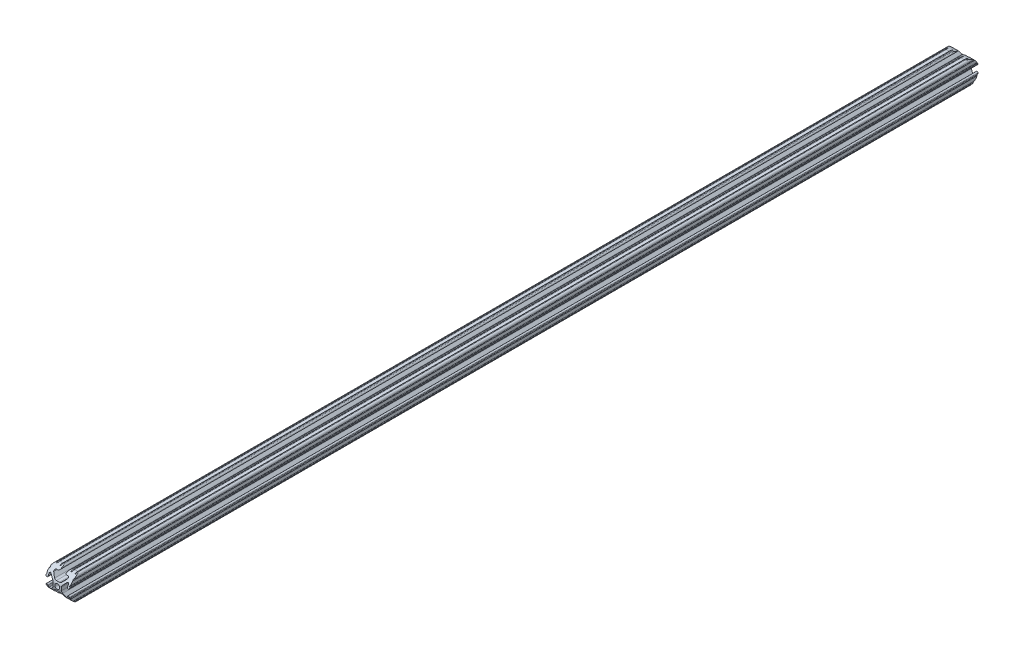
SolidWorks part; units mm, degrees
ref_plane "Front Plane" through (0, 0, 0) normal (0, 0, 1) x (1, 0, 0)
ref_plane "Top Plane" through (0, 0, 0) normal (0, 1, 0) x (1, 0, 0)
ref_plane "Right Plane" through (0, 0, 0) normal (1, 0, 0) x (0, 0, -1)
ref_plane "Plane1" through (0, 0, -450.85) normal (0, 0, -1) x (-1, 0, 0)
sketch "Sketch1" plane through (0, 0, -450.85) normal (0, 0, -1) x (-1, 0, 0)
  line L0 (12.7, -9.5504) -> (12.7, -6.3331)
  line L1 (12.7, -5.3171) -> (12.7, -4.3434)
  line L2 (10.4902, -4.3434) -> (10.4902, -6.4748)
  line L3 (8.7558, -7.1932) -> (5.4257, -3.8632)
  line L4 (4.4958, -1.6181) -> (4.4958, 1.6181)
  line L5 (5.4257, 3.8632) -> (8.7558, 7.1932)
  line L6 (10.4902, 6.4748) -> (10.4902, 4.3434)
  line L7 (12.7, 4.3434) -> (12.7, 5.3171)
  line L8 (12.7, 6.3331) -> (12.7, 9.5504)
  line L9 (9.5504, 12.7) -> (6.3331, 12.7)
  line L10 (5.3171, 12.7) -> (4.3434, 12.7)
  line L11 (4.3434, 10.4902) -> (6.4748, 10.4902)
  line L12 (7.1932, 8.7558) -> (3.8632, 5.4257)
  line L13 (1.6181, 4.4958) -> (-1.6181, 4.4958)
  line L14 (-3.8632, 5.4257) -> (-7.1932, 8.7558)
  line L15 (-6.4748, 10.4902) -> (-4.3434, 10.4902)
  line L16 (-4.3434, 12.7) -> (-5.3171, 12.7)
  line L17 (-6.3331, 12.7) -> (-9.5504, 12.7)
  line L18 (-12.7, 9.5504) -> (-12.7, 6.3331)
  line L19 (-12.7, 5.3171) -> (-12.7, 4.3434)
  line L20 (-10.4902, 4.3434) -> (-10.4902, 6.4748)
  line L21 (-8.7558, 7.1932) -> (-5.4257, 3.8632)
  line L22 (-4.4958, 1.6181) -> (-4.4958, -1.6181)
  line L23 (-5.4257, -3.8632) -> (-8.7558, -7.1932)
  line L24 (-10.4902, -6.4748) -> (-10.4902, -4.3434)
  line L25 (-12.7, -4.3434) -> (-12.7, -5.3171)
  line L26 (-12.7, -6.3331) -> (-12.7, -9.5504)
  line L27 (-9.5504, -12.7) -> (-6.3331, -12.7)
  line L28 (-5.3171, -12.7) -> (-4.3434, -12.7)
  line L29 (-4.3434, -10.4902) -> (-6.4748, -10.4902)
  line L30 (-7.1932, -8.7558) -> (-3.8632, -5.4257)
  line L31 (-1.6181, -4.4958) -> (1.6181, -4.4958)
  line L32 (3.8632, -5.4257) -> (7.1932, -8.7558)
  line L33 (6.4748, -10.4902) -> (4.3434, -10.4902)
  line L34 (4.3434, -12.7) -> (5.3171, -12.7)
  line L35 (6.3331, -12.7) -> (9.5504, -12.7)
  arc A0 (12.6998, -10.5664) -> (12.7, -9.5504) centre (12.7, -10.0584) cw
  arc A1 (12.7, -6.3331) -> (12.7, -5.3171) centre (12.7, -5.8251) cw
  arc A2 (12.7, -4.3434) -> (10.4902, -4.3434) centre (11.5951, -4.3434) ccw
  arc A3 (10.4902, -6.4748) -> (8.7558, -7.1932) centre (9.4742, -6.4748) cw
  arc A4 (5.4257, -3.8632) -> (4.4958, -1.6181) centre (7.6708, -1.6181) cw
  arc A5 (4.4958, 1.6181) -> (5.4257, 3.8632) centre (7.6708, 1.6181) cw
  arc A6 (8.7558, 7.1932) -> (10.4902, 6.4748) centre (9.4742, 6.4748) cw
  arc A7 (10.4902, 4.3434) -> (12.7, 4.3434) centre (11.5951, 4.3434) ccw
  arc A8 (12.7, 5.3171) -> (12.7, 6.3331) centre (12.7, 5.8251) cw
  arc A9 (12.7, 9.5504) -> (12.6998, 10.5664) centre (12.7, 10.0584) cw
  arc A10 (12.6998, 10.5664) -> (10.5664, 12.6998) centre (10.5918, 10.5918) ccw
  arc A11 (10.5664, 12.6998) -> (9.5504, 12.7) centre (10.0584, 12.7) cw
  arc A12 (6.3331, 12.7) -> (5.3171, 12.7) centre (5.8251, 12.7) cw
  arc A13 (4.3434, 12.7) -> (4.3434, 10.4902) centre (4.3434, 11.5951) ccw
  arc A14 (6.4748, 10.4902) -> (7.1932, 8.7558) centre (6.4748, 9.4742) cw
  arc A15 (3.8632, 5.4257) -> (1.6181, 4.4958) centre (1.6181, 7.6708) cw
  arc A16 (-1.6181, 4.4958) -> (-3.8632, 5.4257) centre (-1.6181, 7.6708) cw
  arc A17 (-7.1932, 8.7558) -> (-6.4748, 10.4902) centre (-6.4748, 9.4742) cw
  arc A18 (-4.3434, 10.4902) -> (-4.3434, 12.7) centre (-4.3434, 11.5951) ccw
  arc A19 (-5.3171, 12.7) -> (-6.3331, 12.7) centre (-5.8251, 12.7) cw
  arc A20 (-9.5504, 12.7) -> (-10.5664, 12.6998) centre (-10.0584, 12.7) cw
  arc A21 (-10.5664, 12.6998) -> (-12.6998, 10.5664) centre (-10.5918, 10.5918) ccw
  arc A22 (-12.6998, 10.5664) -> (-12.7, 9.5504) centre (-12.7, 10.0584) cw
  arc A23 (-12.7, 6.3331) -> (-12.7, 5.3171) centre (-12.7, 5.8251) cw
  arc A24 (-12.7, 4.3434) -> (-10.4902, 4.3434) centre (-11.5951, 4.3434) ccw
  arc A25 (-10.4902, 6.4748) -> (-8.7558, 7.1932) centre (-9.4742, 6.4748) cw
  arc A26 (-5.4257, 3.8632) -> (-4.4958, 1.6181) centre (-7.6708, 1.6181) cw
  arc A27 (-4.4958, -1.6181) -> (-5.4257, -3.8632) centre (-7.6708, -1.6181) cw
  arc A28 (-8.7558, -7.1932) -> (-10.4902, -6.4748) centre (-9.4742, -6.4748) cw
  arc A29 (-10.4902, -4.3434) -> (-12.7, -4.3434) centre (-11.5951, -4.3434) ccw
  arc A30 (-12.7, -5.3171) -> (-12.7, -6.3331) centre (-12.7, -5.8251) cw
  arc A31 (-12.7, -9.5504) -> (-12.6998, -10.5664) centre (-12.7, -10.0584) cw
  arc A32 (-12.6998, -10.5664) -> (-10.5664, -12.6998) centre (-10.5918, -10.5918) ccw
  arc A33 (-10.5664, -12.6998) -> (-9.5504, -12.7) centre (-10.0584, -12.7) cw
  arc A34 (-6.3331, -12.7) -> (-5.3171, -12.7) centre (-5.8251, -12.7) cw
  arc A35 (-4.3434, -12.7) -> (-4.3434, -10.4902) centre (-4.3434, -11.5951) ccw
  arc A36 (-6.4748, -10.4902) -> (-7.1932, -8.7558) centre (-6.4748, -9.4742) cw
  arc A37 (-3.8632, -5.4257) -> (-1.6181, -4.4958) centre (-1.6181, -7.6708) cw
  arc A38 (1.6181, -4.4958) -> (3.8632, -5.4257) centre (1.6181, -7.6708) cw
  arc A39 (7.1932, -8.7558) -> (6.4748, -10.4902) centre (6.4748, -9.4742) cw
  arc A40 (4.3434, -10.4902) -> (4.3434, -12.7) centre (4.3434, -11.5951) ccw
  arc A41 (5.3171, -12.7) -> (6.3331, -12.7) centre (5.8251, -12.7) cw
  arc A42 (9.5504, -12.7) -> (10.5664, -12.6998) centre (10.0584, -12.7) cw
  arc A43 (10.5664, -12.6998) -> (12.6998, -10.5664) centre (10.5918, -10.5918) ccw
  circle A44 centre (0, 0) radius 2.6035
extrude "Boss-Extrude1" add sketch "Sketch1" against normal mid plane 980.44
sketch "Sketch2" plane through (12.7, 0, 0) normal (1, 0, 0) x (0, 0, -1)
  line L5 (-26.7737, 12.6998) -> (-26.7737, 15.4074)
  line L8 (-26.7737, 15.4074) -> (-42.7243, 14.8358)
  line L9 (-42.7243, 14.8358) -> (-41.6963, -13.8481)
  line L10 (-41.6963, -13.8481) -> (-26.7737, -13.8481)
  line L11 (-26.7737, -13.8481) -> (-26.7737, -12.6998)
  line L13 (928.3702, 16.3192) -> (945.3572, 16.3192)
  line L14 (945.3572, 16.3192) -> (945.3572, -13.8481)
  line L15 (945.3572, -13.8481) -> (928.3702, -13.8481)
  line L16 (928.3702, -13.8481) -> (928.3702, -12.6998)
  line L17 (928.3702, 16.3192) -> (928.3702, 12.6998)
  arc A0 (-26.7737, 12.6998) -> (-26.7737, -12.6998) centre (-26.7737, 0) ccw
  arc A1 (928.3702, -12.6998) -> (928.3702, 12.6998) centre (928.3702, 0) ccw
extrude "Cut-Extrude1" cut sketch "Sketch2" against normal through all
